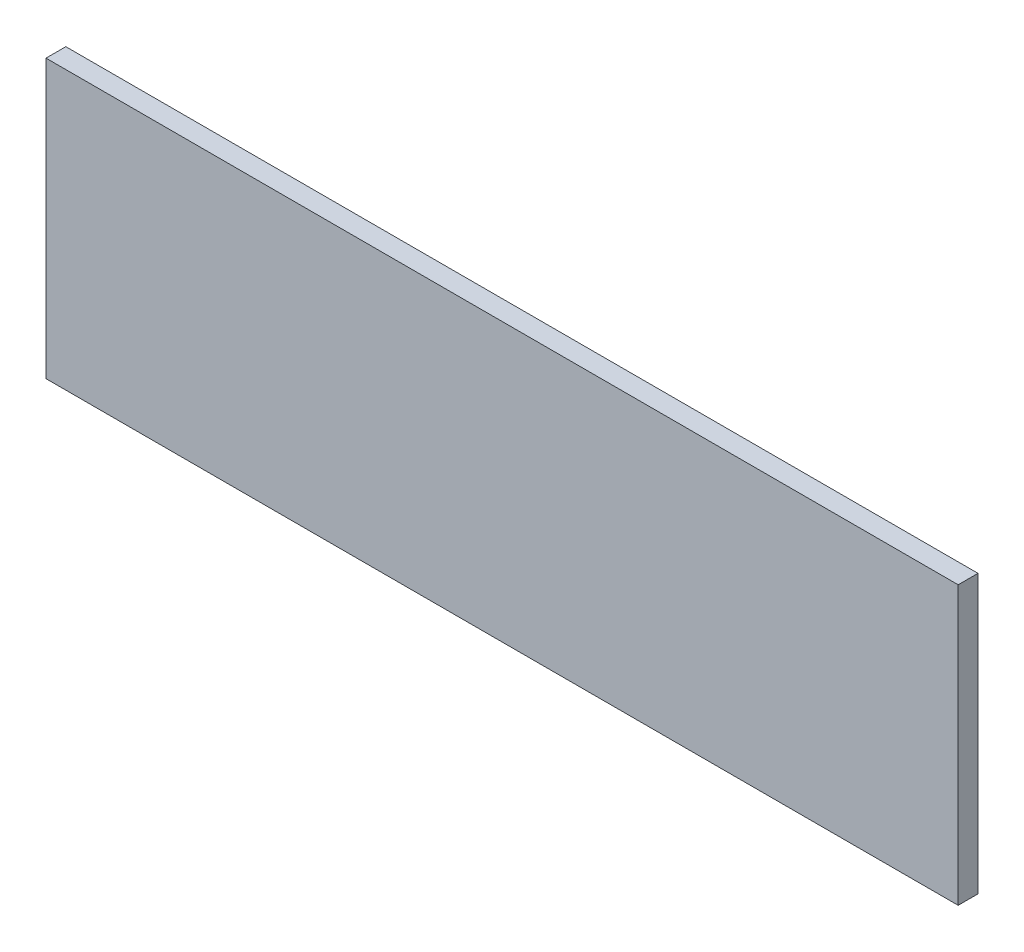
SolidWorks part; units mm, degrees
ref_plane "Front Plane" through (0, 0, 0) normal (0, 0, 1) x (1, 0, 0)
ref_plane "Top Plane" through (0, 0, 0) normal (0, 1, 0) x (1, 0, 0)
ref_plane "Right Plane" through (0, 0, 0) normal (1, 0, 0) x (0, 0, -1)
sketch "Sketch1" plane through (0, 0, 0) normal (0, 0, 1) x (1, 0, 0)
  line L1 (0, 0) -> (292.1, 0)
  line L2 (0, 0) -> (0, 88.9)
  line L3 (0, 88.9) -> (292.1, 88.9)
  line L4 (292.1, 0) -> (292.1, 88.9)
  dimension "D1" = 292.1
  dimension "D2" = 88.9
extrude "Boss-Extrude1" add sketch "Sketch1" along normal blind 6.35 contours L3 L4 L1 L2
